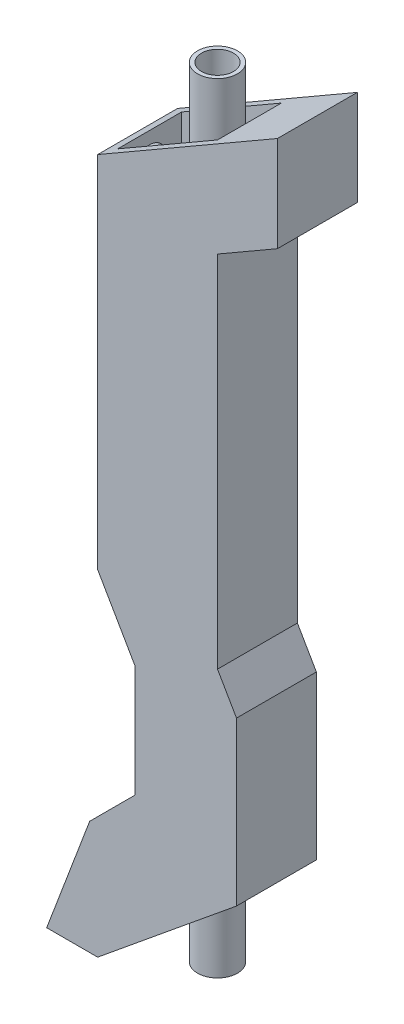
SolidWorks part; units mm, degrees
ref_plane "Front Plane" through (0, 0, 0) normal (0, 0, 1) x (1, 0, 0)
ref_plane "Top Plane" through (0, 0, 0) normal (0, 1, 0) x (1, 0, 0)
ref_plane "Right Plane" through (0, 0, 0) normal (1, 0, 0) x (0, 0, -1)
sketch "Sketch2" plane through (0, 0, 0) normal (0, 0, 1) x (1, 0, 0)
  line L1 (25, 125.9808) -> (-20, 100)
  line L2 (-20, 100) -> (-20, 10)
  line L10 (10, 3.4313) -> (10, 93.4313)
  line L11 (10, 93.4313) -> (25, 102.0915)
  line L12 (25, 102.0915) -> (25, 125.9808)
  line L15 (-20, 10) -> (-10.6295, -6.2302)
  line L16 (-10.6295, -6.2302) -> (-10.6295, -35.4869)
  line L21 (10, 3.4313) -> (14.754, -4.8029)
  line L22 (14.754, -4.8029) -> (14.754, -45.5507)
  line L23 (14.754, -45.5507) -> (-20, -74.0192)
  line L24 (-10.6295, -34.1776) -> (-22.0026, -45.5507)
  line L25 (-22.0026, -45.5507) -> (-32.764, -74.0192)
  line L26 (-32.764, -74.0192) -> (-20, -74.0192)
  dimension "D1" = 200
  dimension "D4" = 90
  dimension "D5" = 120
  dimension "D6" = 30
  dimension "D7" = 90
extrude "Boss-Extrude1" add sketch "Sketch2" along normal mid plane 20
ref_plane "Plane1" through (0, 100, 0) normal (0, 1, 0) x (1, 0, 0)
sketch "Sketch4" plane through (0, 100, 0) normal (0, 1, 0) x (1, 0, 0)
  line L1 (-17, -8) -> (8, -8)
  line L2 (-17, -8) -> (-17, 8)
  line L3 (-17, 8) -> (8, 8)
  line L4 (8, -8) -> (8, 8)
  line L5 (-17, -8) -> (8, 8) construction
  line L6 (-17, 8) -> (8, -8) construction
  line L7 (25, 10) -> (-20, 10) construction
  line L9 (-20, -10) -> (-20, 10) construction
  point P0 (-4.5, 0)
  dimension "D1" = 16
  dimension "D2" = 25
  dimension "D3" = 2
  dimension "D4" = 3
extrude "Cut-Extrude1" cut sketch "Sketch4" against normal blind 89 and the other way blind 20
sketch "Sketch5" plane through (0, 100, 0) normal (0, 1, 0) x (1, 0, 0)
  circle A0 centre (0, 0) radius 5
  dimension "D1" = 10
extrude "Boss-Extrude2" add sketch "Sketch5" along normal blind 25 and the other way blind 10 separate body
sketch "Sketch7" plane through (0, 0, 0) normal (1, 0, 0) x (0, 0, -1)
  circle A0 centre (0, 94.6191) radius 4
  dimension "D1" = 8
extrude "Boss-Extrude3" add sketch "Sketch7" along normal blind 10 and the other way blind 18
sketch "Sketch8" plane through (0, 125, 0) normal (0, 1, 0) x (1, 0, 0)
  circle A0 centre (0, 0) radius 4
  dimension "D1" = 8
extrude "Cut-Extrude2" cut sketch "Sketch8" against normal blind 25
ref_plane "Plane2" through (0, -40, 0) normal (0, 1, 0) x (1, 0, 0)
sketch "Sketch9" plane through (0, -40, 0) normal (0, 1, 0) x (1, 0, 0)
  line L1 (-10.4673, 8.4936) -> (13.5327, 8.4936)
  line L2 (-10.4673, 8.4936) -> (-10.4673, -8.5064)
  line L3 (-10.4673, -8.5064) -> (13.5327, -8.5064)
  line L4 (13.5327, 8.4936) -> (13.5327, -8.5064)
  line L5 (-10.4673, 8.4936) -> (13.5327, -8.5064) construction
  line L6 (-10.4673, -8.5064) -> (13.5327, 8.4936) construction
  point P0 (1.5327, -0.0064)
  dimension "D1" = 17
  dimension "D2" = 24
extrude "Cut-Extrude3" cut sketch "Sketch9" against normal blind 28 and the other way blind 32
sketch "Sketch11" plane through (0, -40, 0) normal (0, 1, 0) x (1, 0, 0)
  circle A0 centre (0, 0) radius 5
  circle A1 centre (0, 0) radius 4
extrude "Boss-Extrude4" add sketch "Sketch11" along normal blind 10 and the other way blind 30 separate body
